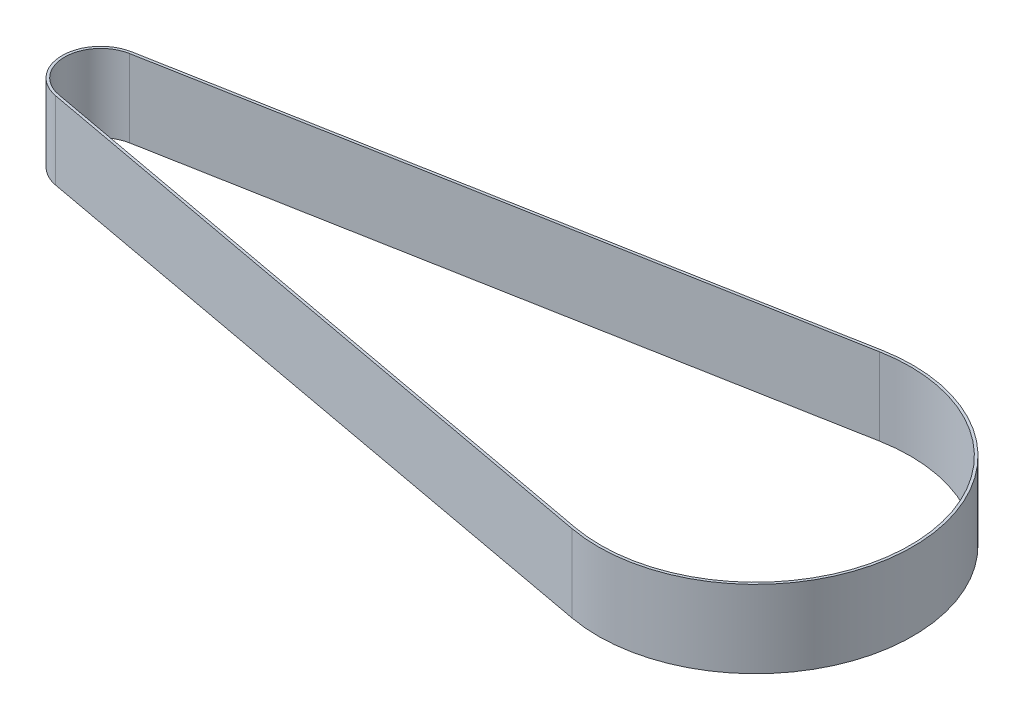
SolidWorks part; units mm, degrees
ref_plane "Front Plane" through (0, 0, 0) normal (0, 0, 1) x (1, 0, 0)
ref_plane "Top Plane" through (0, 0, 0) normal (0, 1, 0) x (1, 0, 0)
ref_plane "Right Plane" through (0, 0, 0) normal (1, 0, 0) x (0, 0, -1)
sketch "Sketch1" plane through (0, 0, 0) normal (0, 1, 0) x (1, 0, 0)
  line L0 (-1.2687, 6.8841) -> (121.4626, 29.5031)
  line L1 (-27.1312, 0) -> (179.3781, 0) construction
  line L2 (-1.2687, -6.8841) -> (121.4626, -29.5031)
  line L3 (-1.3593, 7.3758) -> (121.372, 29.9949)
  line L4 (-1.3593, -7.3758) -> (121.372, -29.9949)
  arc A0 (-1.2687, 6.8841) -> (-1.2687, -6.8841) centre (0, 0) ccw
  arc A1 (121.4626, -29.5031) -> (121.4626, 29.5031) centre (126.9, 0) ccw
  arc A2 (121.372, -29.9949) -> (121.372, 29.9949) centre (126.9, 0) ccw
  arc A3 (-1.3593, 7.3758) -> (-1.3593, -7.3758) centre (0, 0) ccw
  dimension "D1" = 14
  dimension "D2" = 60
  dimension "D3" = 126.9
  dimension "D4" = 0.5
extrude "Boss-Extrude1" add sketch "Sketch1" along normal blind 15
